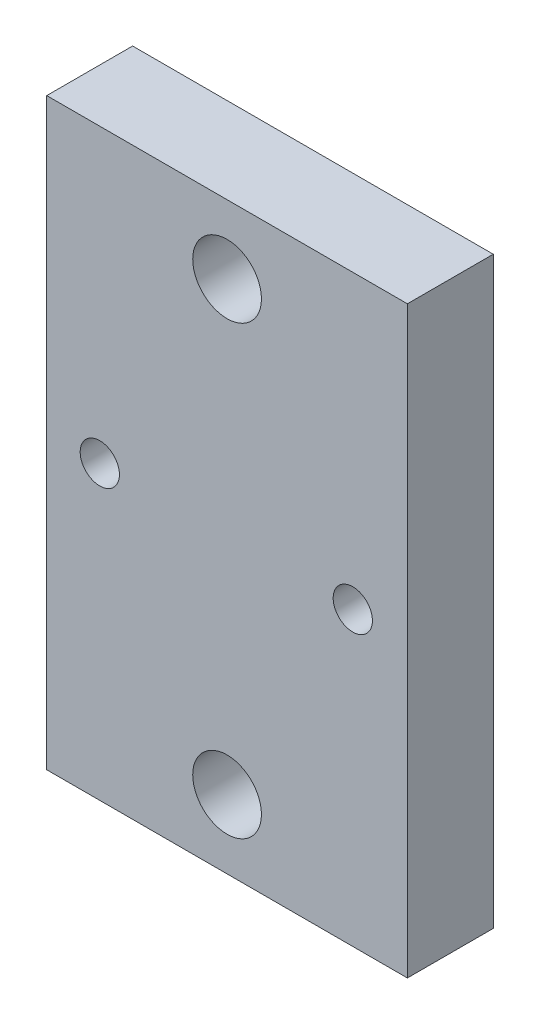
SolidWorks part; units mm, degrees
ref_plane "Front Plane" through (0, 0, 0) normal (0, 0, 1) x (1, 0, 0)
ref_plane "Top Plane" through (0, 0, 0) normal (0, 1, 0) x (1, 0, 0)
ref_plane "Right Plane" through (0, 0, 0) normal (1, 0, 0) x (0, 0, -1)
sketch "Sketch1" plane through (0, 0, 0) normal (0, 0, 1) x (1, 0, 0)
  line L1 (-10.5, 17) -> (10.5, 17)
  line L2 (-10.5, 17) -> (-10.5, -17)
  line L3 (-10.5, -17) -> (10.5, -17)
  line L4 (10.5, 17) -> (10.5, -17)
  dimension "D1" = 34
  dimension "D2" = 21
  dimension "D3" = 17
  dimension "D4" = 10.5
extrude "Boss-Extrude1" add sketch "Sketch1" along normal blind 5
sketch "Sketch2" plane through (0, 0, 0) normal (0, 0, -1) x (-1, 0, 0)
  line L0 (0, 0) -> (-11.4611, 0) construction
  line L1 (0, 0) -> (0, -6.3634) construction
  circle A1 centre (7.4115, 0) radius 1.143
  circle A3 centre (-7.3205, 0) radius 1.143
  dimension "D2" = 2.286
  dimension "D3" = 2.286
  dimension "D4" = 14.732
  dimension "D1" = 7.3205
sketch "Sketch3" plane through (0, 0, 0) normal (0, 0, -1) x (-1, 0, 0)
  line L0 (0, 0) -> (-9.2664, 0) construction
  line L1 (0, 0) -> (0, -7.6546) construction
  circle A1 centre (0, -13) radius 2
  circle A3 centre (0, 13) radius 2
  dimension "D2" = 4
  dimension "D3" = 4
  dimension "D1" = 13
  dimension "D4" = 26
extrude "Cut-Extrude1" cut sketch "Sketch2" against normal blind 10
extrude "Cut-Extrude2" cut sketch "Sketch3" against normal blind 10
